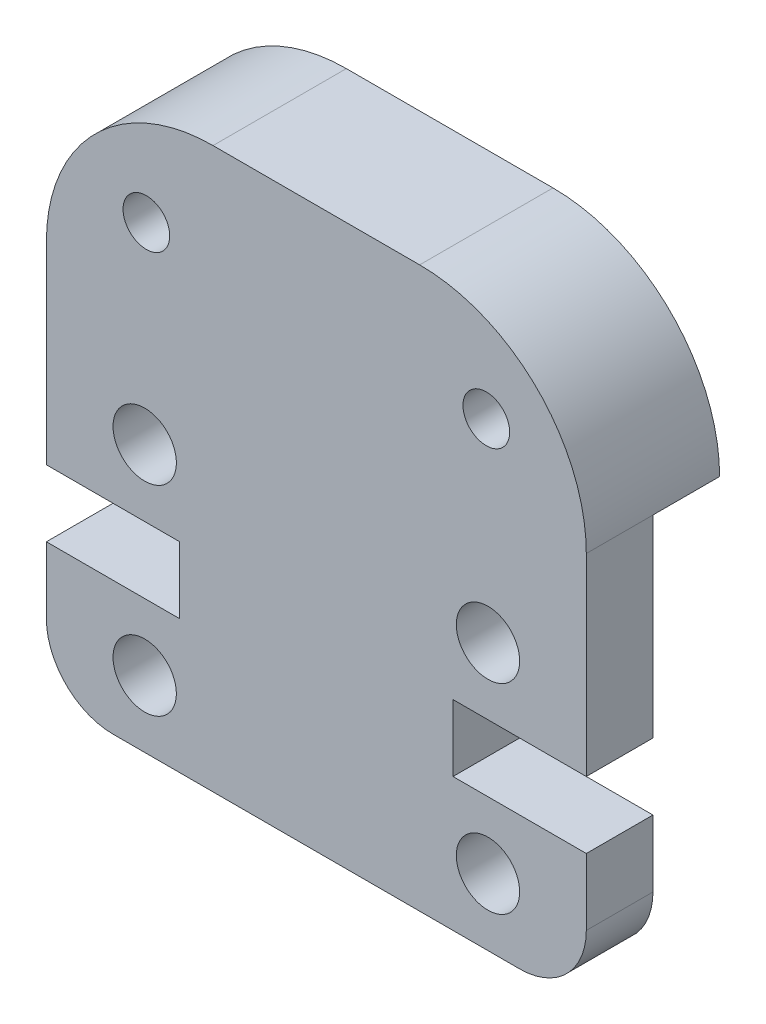
SolidWorks part; units mm, degrees
ref_plane "Front Plane" through (0, 0, 0) normal (0, 0, 1) x (1, 0, 0)
ref_plane "Top Plane" through (0, 0, 0) normal (0, 1, 0) x (1, 0, 0)
ref_plane "Right Plane" through (0, 0, 0) normal (1, 0, 0) x (0, 0, -1)
sketch "Sketch1" plane through (0, 0, 0) normal (0, 0, 1) x (1, 0, 0)
  line L0 (0, 6) -> (0, 11.795)
  line L1 (12.2, 4) -> (16.2, 4)
  line L2 (5, 16.795) -> (11.2, 16.795)
  line L3 (2, 0) -> (14.2, 0)
  line L4 (12.2, 6) -> (12.2, 4)
  line L5 (0, 2) -> (0, 4)
  line L6 (0, 6) -> (4, 6)
  line L7 (16.2, 6) -> (12.2, 6)
  line L8 (4, 6) -> (4, 4)
  line L9 (4, 4) -> (0, 4)
  line L10 (16.2, 2) -> (16.2, 4)
  line L11 (16.2, 6) -> (16.2, 11.795)
  line L12 (8.1, 16.795) -> (8.1, 0) construction
  circle A0 centre (13.25, 2) radius 0.95
  arc A1 (5, 16.795) -> (0, 11.795) centre (5, 11.795) ccw
  circle A2 centre (13.25, 8) radius 0.95
  circle A3 centre (3, 13.795) radius 0.7
  arc A4 (16.2, 2) -> (14.2, 0) centre (14.2, 2) cw
  arc A5 (0, 2) -> (2, 0) centre (2, 2) ccw
  circle A6 centre (13.2, 13.795) radius 0.7
  circle A7 centre (2.95, 8) radius 0.95
  arc A8 (11.2, 16.795) -> (16.2, 11.795) centre (11.2, 11.795) cw
  circle A9 centre (2.95, 2) radius 0.95
  dimension "D1" = 1.9
  dimension "D2" = 1.4
  dimension "D3" = 5
  dimension "D4" = 2
  dimension "D5" = 3
  dimension "D6" = 8.1
  dimension "D7" = 8
  dimension "D8" = 3
  dimension "D9" = 16.795
extrude "Boss-Extrude1" add sketch "Sketch1" along normal blind 4
sketch "Sketch2" plane through (0, 0, 0) normal (0, 0, 1) x (1, 0, 0)
  line L0 (0, 0) -> (0, 11.795)
  line L1 (0, 11.795) -> (16.2, 11.795)
  line L2 (16.2, 11.795) -> (16.2, 0)
  line L3 (16.2, 0) -> (0, 0)
extrude "Cut-Extrude1" cut sketch "Sketch2" along normal blind 2
equation "\"D6@Sketch1\"= \"fingerWidth@parametersSketch@prostheticParameters.SLDPRT\" / 2 'DIP width"
equation "\"D9@Sketch1\"= \"HL@parametersSketch@prostheticParameters.SLDPRT\" * 0.107 - 3 'DIP length - Sil. Sht DIP"
equation "\"D1@Sketch1\"= 1.5 + \"tol1@parametersSketch@prostheticParameters.SLDPRT\""
equation "\"D2@Sketch1\"= 1 + \"tol1@parametersSketch@prostheticParameters.SLDPRT\""
